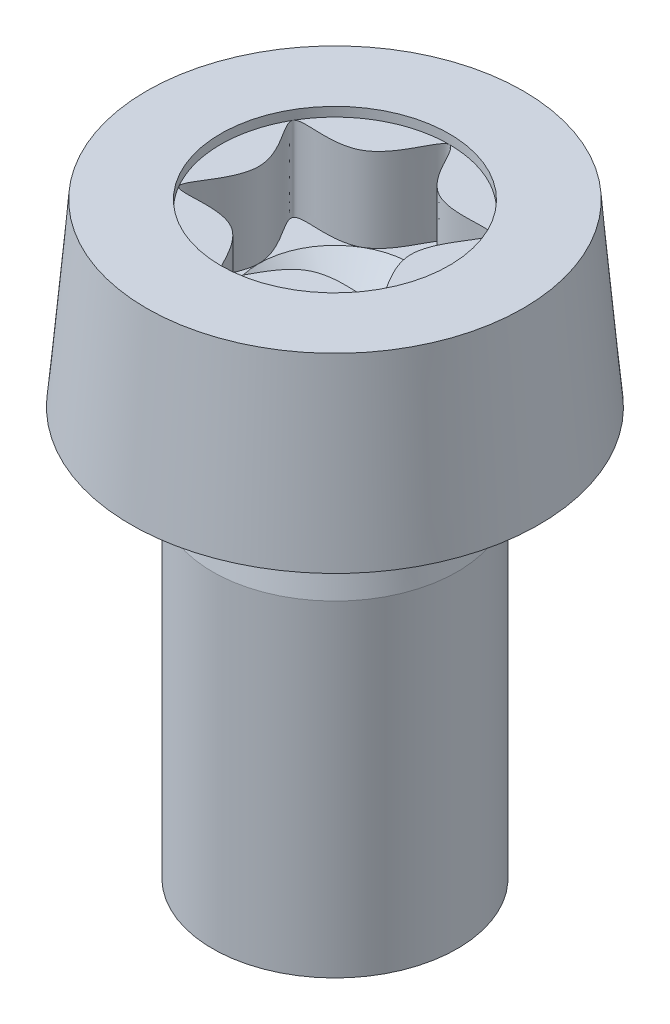
SolidWorks part; units mm, degrees
material "AISI 316L Acero inoxidable"
ref_plane "Front" through (0, 0, 0) normal (0, 0, 1) x (1, 0, 0)
ref_plane "Top" through (0, 0, 0) normal (0, 1, 0) x (1, 0, 0)
ref_plane "Right" through (0, 0, 0) normal (1, 0, 0) x (0, 0, -1)
sketch "Sketch1" plane through (0, 0, 0) normal (0, 0, 1) x (1, 0, 0)
  line L0 (0, 0) -> (0, 5.1006) construction
  line L1 (0, 14.4) -> (4.615, 14.4)
  line L2 (4.615, 14.4) -> (5, 10)
  line L3 (5, 10) -> (3, 10)
  line L4 (3, 0) -> (3, 8)
  line L5 (3, 0) -> (0, 0)
  line L6 (0, 0) -> (0, 14.4)
  line L7 (5, 10) -> (5, 9) construction
  line L8 (3, 8) -> (2.6, 10)
  line L9 (2.6, 10) -> (3, 10)
  line L10 (5, 9) -> (5, 1) construction
  dimension "length" = 10
  dimension "head_ht" = 4.4
  dimension "head_dia" = 10
  dimension "dia" = 6
  dimension "D1" = 5
  dimension "pitch" = 1
  dimension "thread_gap" = 2
  dimension "D2" = 0.4
  dimension "thread_length" = 8
revolve "Body-Revolve" add sketch "Sketch1" angle 360 about L0
cosmetic thread "ThreadCosmetic" [suppressed] parameters "D1"=8, "D2"=4.9175
fillet "Fillet1" radius 0.25 1 edges at (0, 10, -2.6)
sketch "Sketch2" plane through (0, 14.4, 0) normal (0, 1, 0) x (-1, 0, 0)
  line L0 (0, -3.08) -> (0, 0)
  line L1 (0, 0) -> (-1.4, -2.4249)
  circle A0 centre (0, 0) radius 2.8
  circle A1 centre (0, 0) radius 1.8667
  spline S0 degree 3 poles (0.6039, -1.046) (0, -3.677) (-0.6039, -1.046) (-3.1844, -1.8385) (-1.2078, 0) (-3.1844, 1.8385) (-0.6039, 1.046) (0, 3.677) (0.6039, 1.046) (3.1844, 1.8385) (1.2078, 0) (3.1844, -1.8385) (0.6039, -1.046) (0, -3.677) (-0.6039, -1.046) knots -0.25 -0.166667 -0.083333 0 0.083333 0.166667 0.25 0.333333 0.416667 0.5 0.583333 0.666667 0.75 0.833333 0.916667 1 1.083333 1.166667 1.25 only from (0, -2.8) to (0, -2.8)
  point P5 (0, -2.8)
  point P7 (-0.9333, -1.6166)
  point P10 (-2.4249, -1.4)
  point P11 (-2.4249, 1.4)
  point P12 (0, 2.8)
  point P13 (2.4249, 1.4)
  point P14 (2.4249, -1.4)
  point P15 (-1.8667, 0)
  point P16 (-0.9333, 1.6166)
  point P17 (0.9333, 1.6166)
  point P18 (1.8667, 0)
  point P19 (0.9333, -1.6166)
  dimension "socket_dia" = 5.6
  dimension "D1" = 3.7333
  dimension "D2" = 3.08
  dimension "D3" = 30
extrude "Socket-Cut-Extrude1" cut sketch "Sketch2" against normal blind 2.29 contours S0
sketch "Sketch3" plane through (0, 14.4, 0) normal (0, 1, 0) x (-1, 0, 0)
  circle A0 centre (0, 0) radius 2.8
  dimension "D1" = 5.6
extrude "Socket-Cut-Extrude2" cut sketch "Sketch3" against normal blind 0.229
sketch "Sketch4" plane through (0, 0, 0) normal (0, 0, 1) x (1, 0, 0)
  line L0 (0, 12.11) -> (1.8667, 12.11)
  line L1 (2.4353, 12.11) -> (-2.4353, 12.11) construction
  line L2 (1.8667, 12.11) -> (0, 10.44)
  line L3 (0, 0) -> (0, 5.1006) construction
  line L4 (0, 10.44) -> (0, 12.11)
  line L5 (2.8, 14.4) -> (-2.8, 14.4) construction
  dimension "D1" = 3.96
  dimension "D2" = 1.8667
revolve "Drill-Cut-Revolve" cut sketch "Sketch4" angle 360 about axis through (0, 0, 0) along (0, 1, 0)
sketch "Sketch5" plane through (0, 0, 0) normal (0, 0, 1) x (1, 0, 0)
  line L0 (3, 0) -> (2.4588, 0.3125)
  line L1 (2.4588, 0.3125) -> (3, 0.625)
  line L2 (3, 0) -> (3, 8) construction
  line L3 (3, 0.625) -> (3, 0)
  line L4 (0, 0) -> (0, 5.1006) construction
  dimension "D1" = 2.4588
revolve "ThreadSchematic" [suppressed] cut sketch "Sketch5" angle 360 about axis through (0, 0, 0) along (0, 1, 0)
pattern_linear "ThdSchPat" [suppressed] count 8 spacing 1 along (0, 1, 0)
equation "\"D2@Sketch1\" = 0.2*\"thread_gap@Sketch1\""
equation "\"D1@Sketch2\" = \"socket_dia@Sketch2\" / 1.5"
equation "\"D2@Sketch2\" = \"socket_dia@Sketch2\" / 2 * 1.1"
equation "\"D1@Sketch3\" =\"socket_dia@Sketch2\""
equation "\"D1@Socket-Cut-Extrude2\" = .1 * \"socket_dep@Socket-Cut-Extrude1\""
equation "\"D1@Sketch4\" = 0.9*\"head_ht@Sketch1\""
equation "\"D2@Sketch4\" = \"D1@Sketch2\" / 2"
equation "\"D1@ThreadCosmetic\" = \"thread_length@Sketch1\""
equation "\"D2@ThreadCosmetic\" = \"dia@Sketch1\" - 1.0825 * \"pitch@Sketch1\""
equation "\"D1@Sketch5\" = \"D2@ThreadCosmetic\" / 2"
equation "\"D3@ThdSchPat\" = \"pitch@Sketch1\""
equation "\"D1@ThdSchPat\" = \"thread_length@Sketch1\" / \"pitch@Sketch1\""
